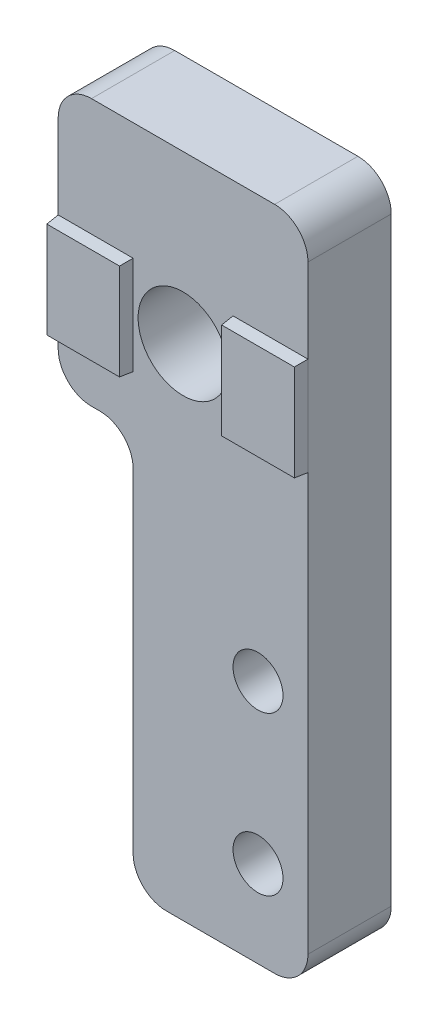
SolidWorks part; units mm, degrees
material "ABS"
ref_plane "Front Plane" through (0, 0, 0) normal (0, 0, 1) x (1, 0, 0)
ref_plane "Top Plane" through (0, 0, 0) normal (0, 1, 0) x (1, 0, 0)
ref_plane "Right Plane" through (0, 0, 0) normal (1, 0, 0) x (0, 0, -1)
sketch "Sketch1" plane through (0, 0, 0) normal (0, 0, 1) x (1, 0, 0)
  line L0 (0, -2) -> (0, -14)
  line L1 (2, 0) -> (13, 0)
  line L2 (6.5, -40) -> (13, -40)
  line L3 (15, -2) -> (15, -38)
  line L6 (7.5, 20) -> (7.5, -40) construction
  line L8 (2, -16) -> (2.5, -16)
  line L9 (4.5, -38) -> (4.5, -18)
  circle A0 centre (7.5, -10) radius 2.7
  circle A1 centre (12, -34.8) radius 1.5
  circle A2 centre (12, -25.3) radius 1.5
  arc A3 (15, -38) -> (13, -40) centre (13, -38) cw
  arc A4 (6.5, -40) -> (4.5, -38) centre (6.5, -38) cw
  arc A5 (0, -2) -> (2, 0) centre (2, -2) cw
  arc A6 (13, 0) -> (15, -2) centre (13, -2) cw
  arc A7 (4.5, -18) -> (2.5, -16) centre (2.5, -18) ccw
  arc A8 (2, -16) -> (0, -14) centre (2, -14) cw
  point P1 (0, 0)
  point P20 (0, -40)
  point P23 (0, 0)
  point P26 (15, 0)
  dimension "D3" = 5.4
  dimension "D4" = 10
  dimension "D5" = 9.5
  dimension "D6" = 5.2
  dimension "D7" = 3
  dimension "D8" = 3
  dimension "D12" = 2
  dimension "D13" = 2
  dimension "D1" = 15
  dimension "D2" = 40
  dimension "D9" = 16
  dimension "D10" = 10.5
  dimension "D11" = 7.5
extrude "Boss-Extrude1" add sketch "Sketch1" along normal blind 5
sketch "Sketch2" plane through (0, 0, 5) normal (0, 0, 1) x (1, 0, 0)
  line L0 (0, -2) -> (0, -14) construction
  line L1 (0, -7.05) -> (4.5, -7.05)
  line L2 (0, -7.05) -> (0, -12.95)
  line L3 (0, -12.95) -> (4.5, -12.95)
  line L4 (4.5, -7.05) -> (4.5, -12.95)
  line L5 (7.5, 0) -> (7.5, -40) construction
  line L6 (13, 0) -> (2, 0) construction
  line L8 (0, -10) -> (15, -10) construction
  line L9 (15, -38) -> (15, -2) construction
  line L10 (15, -12.95) -> (10.5, -12.95)
  line L11 (15, -7.05) -> (15, -12.95)
  line L12 (15, -7.05) -> (10.5, -7.05)
  line L13 (10.5, -7.05) -> (10.5, -12.95)
  line L14 (6.5, -40) -> (13, -40) construction
  point P10 (7.5, 0)
  dimension "D1" = 10
  dimension "D2" = 5.9
  dimension "D3" = 4.5
extrude "Boss-Extrude2" add sketch "Sketch2" along normal blind 0.75 draft 5
